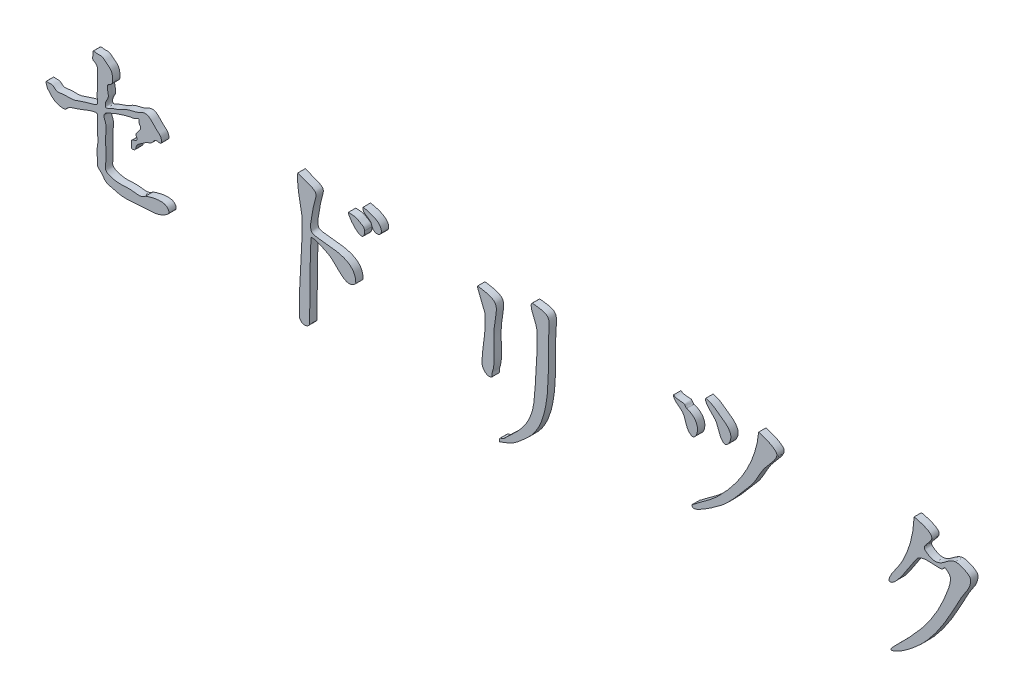
SolidWorks part; units mm, degrees
ref_plane "Plan de face" through (0, 0, 0) normal (0, 0, 1) x (1, 0, 0)
ref_plane "Plan de dessus" through (0, 0, 0) normal (0, 1, 0) x (1, 0, 0)
ref_plane "Plan de droite" through (0, 0, 0) normal (1, 0, 0) x (0, 0, -1)
sketch "Esquisse2" plane through (0, 0, 0) normal (0, 0, 1) x (1, 0, 0)
  line L0 (232.9141, 131.3385) -> (1160.2474, 131.3385) construction
  spline S0 degree 3 poles (432.0808, 148.8385) (430.7718, 149.2574) (428.1607, 149.2105) (428.0808, 147.8385) (426.1031, 113.8895) (427.0708, 79.8306) (426.0808, 45.8385) (425.9892, 42.6952) (421.1449, 40.1314) (418.0808, 40.8385) (415.0863, 41.5295) (412.1299, 44.7657) (412.0808, 47.8385) (411.4511, 87.1894) (416.3283, 126.4834) (416.0808, 165.8385) (416.0785, 166.1982) (407.6157, 203.5133) (410.0808, 215.8385) knots 6 6 6 6 7 7 7 8 8 8 9 9 9 10 10 10 11 11 11 12 12 12 12
  spline S1 degree 3 poles (410.0808, 215.8385) (444.7055, 203.2477) (434.1746, 207.8131) (430.0808, 179.8385) (428.9664, 172.224) (426.3503, 164.337) (428.0808, 156.8385) (430.5024, 146.3446) (489.0808, 160.2947) (489.0808, 124.8385) (489.0808, 124.3671) (488.4141, 124.1718) (488.0808, 123.8385) (475.6539, 111.4116) (464.0342, 132.9607) (453.0808, 139.8385) (446.631, 143.8883) (439.3342, 146.5174) (432.0808, 148.8385) knots 0 0 0 0 1 1 1 2 2 2 3 3 3 4 4 4 5 5 5 6 6 6 6
  spline S2 degree 3 poles (501.0808, 192.8385) (501.0808, 171.0749) (477.8712, 199.0004) (479.0808, 203.8385) knots 2 2 2 2 3 3 3 3
  spline S3 degree 3 poles (479.0808, 203.8385) (487.057, 203.1134) (488.4543, 203.9228) (493.0808, 200.8385) (495.8624, 198.9841) (501.0808, 197.4303) (501.0808, 192.8385) knots 0 0 0 0 1 1 1 2 2 2 2
  spline S4 degree 3 poles (513.0808, 199.8385) (512.205, 200.5391) (510.0802, 206.839) (509.0808, 207.8385) (504.114, 212.8053) (497.4445, 213.2937) (499.0808, 219.8385) knots 2 2 2 2 3 3 3 4 4 4 4
  spline S5 degree 3 poles (499.0808, 219.8385) (504.6438, 219.0438) (513.1693, 216.4461) (517.0808, 213.8385) (530.4477, 204.9272) (521.5423, 193.0693) (513.0808, 199.8385) knots 0 0 0 0 1 1 1 2 2 2 2
  spline S6 degree 3 poles (674.0808, 106.8385) (667.2894, 103.4428) (661.0808, 111.5723) (661.0808, 116.8385) (661.0808, 137.3004) (667.2207, 155.4389) (665.0808, 176.8385) (664.4549, 183.0973) (654.0021, 201.6025) (655.0808, 204.8385) knots 3 3 3 3 4 4 4 5 5 5 6 6 6 6
  spline S7 degree 3 poles (655.0808, 204.8385) (693.7907, 199.9998) (677.0808, 190.2367) (677.0808, 155.8385) (677.0808, 141.4897) (679.6182, 126.451) (675.0808, 112.8385) (674.4396, 110.915) (675.8943, 107.7453) (674.0808, 106.8385) knots 0 0 0 0 1 1 1 2 2 2 3 3 3 3
  spline S8 degree 3 poles (736.0808, 190.8385) (735.8789, 200.2231) (729.0148, 208.4983) (728.0808, 217.8385) (727.9324, 219.3218) (728.5962, 221.9735) (730.0808, 221.8385) (754.1032, 219.6546) (753.4077, 216.0889) (752.0808, 198.8385) (749.2185, 161.6286) (759.794, 94.1709) (724.0808, 60.8385) (704.1065, 42.1958) (701.9448, 42.1625) (685.0808, 35.8385) knots 5 5 5 5 6 6 6 7 7 7 8 8 8 9 9 9 10 10 10 10
  spline S9 degree 3 poles (685.0808, 35.8385) (685.0808, 37.1718) (684.213, 38.8262) (685.0808, 39.8385) (686.536, 41.5362) (689.451, 41.3075) (691.0808, 42.8385) (708.2583, 58.975) (722.0923, 70.4756) (729.0808, 92.8385) (731.6962, 101.208) (732.456, 110.0922) (733.0808, 118.8385) (734.7922, 142.7983) (736.5972, 166.8232) (736.0808, 190.8385) knots 0 0 0 0 1 1 1 2 2 2 3 3 3 4 4 4 5 5 5 5
  spline S10 degree 3 poles (940.0808, 202.8385) (963.1714, 195.1416) (953.7497, 171.1709) (947.0808, 173.8385) (938.4753, 177.2807) (939.3313, 190.0045) (934.0808, 195.8385) (929.9691, 200.4071) (922.0808, 203.6921) (922.0808, 209.8385) knots 3 3 3 3 4 4 4 5 5 5 6 6 6 6
  spline S11 degree 3 poles (922.0808, 209.8385) (923.527, 209.4769) (924.619, 208.1309) (926.0808, 207.8385) (929.3657, 207.1815) (932.7958, 207.4955) (936.0808, 206.8385) (937.9298, 206.4687) (938.2919, 203.4348) (940.0808, 202.8385) knots 0 0 0 0 1 1 1 2 2 2 3 3 3 3
  spline S12 degree 3 poles (992.0808, 186.8385) (984.701, 188.3144) (983.1076, 203.8049) (979.0808, 208.8385) (975.4123, 213.4241) (963.4921, 222.6611) (966.0808, 227.8385) knots 3 3 3 3 4 4 4 5 5 5 5
  spline S13 degree 3 poles (966.0808, 227.8385) (970.8696, 227.0404) (975.5793, 224.4646) (979.0808, 221.8385) (989.3444, 214.1408) (1007.6125, 205.6362) (997.0808, 189.8385) (996.0026, 188.2213) (993.9867, 186.4573) (992.0808, 186.8385) knots 0 0 0 0 1 1 1 2 2 2 3 3 3 3
  spline S14 degree 3 poles (973.0808, 101.8385) (955.3152, 89.9948) (948.0138, 87.1732) (947.0808, 91.8385) (946.8034, 93.2253) (948.9764, 93.955) (950.0808, 94.8385) (960.6506, 103.2943) (972.3486, 110.4307) (982.0808, 119.8385) (1009.9385, 146.7677) (1034.787, 184.3141) (1038.0808, 223.8385) knots 5 5 5 5 6 6 6 7 7 7 8 8 8 9 9 9 9
  spline S15 degree 3 poles (1038.0808, 223.8385) (1045.1995, 221.7029) (1057.4805, 217.9721) (1062.0808, 211.8385) (1066.6736, 205.7148) (1051.0388, 192.4251) (1045.0808, 183.8385) (1038.3328, 174.1135) (1033.929, 162.6994) (1026.0808, 153.8385) (1016.0594, 142.5241) (1006.8695, 130.4237) (996.0808, 119.8385) (989.1315, 113.0204) (981.1811, 107.2387) (973.0808, 101.8385) knots 0 0 0 0 1 1 1 2 2 2 3 3 3 4 4 4 5 5 5 5
  spline S16 degree 3 poles (1224.0808, 64.8385) (1252.2153, 92.2516) (1275.5895, 117.1487) (1291.0808, 153.8385) (1293.5642, 159.7204) (1303.0102, 180.4161) (1298.0808, 185.8385) (1289.2174, 195.5882) (1291.6199, 187.3725) (1287.0808, 186.8385) (1276.4407, 185.5867) (1263.7888, 190.0793) (1255.0808, 183.8385) (1251.0844, 180.9745) (1226.944, 135.7426) (1217.0808, 136.8385) (1214.4098, 137.1353) (1216.85, 142.4495) (1218.0808, 144.8385) (1222.6117, 153.6339) (1229.5921, 161.0214) (1234.0808, 169.8385) (1244.8809, 191.0531) (1248.6675, 207.2262) (1250.0808, 229.8385) knots 8 8 8 8 9 9 9 10 10 10 11 11 11 12 12 12 13 13 13 14 14 14 15 15 15 16 16 16 16
  spline S17 degree 3 poles (1250.0808, 229.8385) (1251.6302, 229.3958) (1274.6718, 224.5227) (1274.0808, 216.8385) (1273.5433, 209.8512) (1259.6339, 202.2479) (1265.0808, 197.8385) (1288.5945, 178.8036) (1294.0532, 211.1568) (1313.0808, 203.8385) (1318.62, 201.708) (1327.2255, 198.7716) (1327.0808, 192.8385) (1326.8081, 181.6615) (1317.1909, 172.7826) (1312.0808, 162.8385) (1297.7982, 135.0455) (1282.3584, 106.7509) (1260.0808, 84.8385) (1257.0039, 81.8121) (1232.7633, 59.3262) (1219.0808, 56.8385) (1215.9868, 56.276) (1221.8285, 62.644) (1224.0808, 64.8385) knots 0 0 0 0 1 1 1 2 2 2 3 3 3 4 4 4 5 5 5 6 6 6 7 7 7 8 8 8 8
  spline S18 degree 3 poles (71.0754, 142.9597) (75.4067, 135.4309) (84.662, 131.0239) (93.2749, 132.3289) knots 0 0 0 0 1 1 1 1
  spline S19 degree 3 poles (93.2749, 132.3289) (97.1532, 137.9943) (107.0232, 139.8388) (120.1737, 145.3167) (127.9688, 148.3887) (138.3028, 150.4256) (136.771, 142.9134) (137.1866, 136.9637) (136.9161, 129.7798) (137.3904, 121.7141) (137.8435, 112.4509) (134.8371, 102.883) (138.1932, 94.7265) (135.799, 86.8932) (143.4968, 82.1954) (146.9939, 74.2276) (157.3244, 71.4208) (169.9252, 67.7133) (185.3121, 68.5902) (201.75, 70.1743) (216.5712, 69.9187) (227.4319, 74.5624) (236.0297, 80.0802) (231.5538, 88.1935) (218.7651, 89.785) (209.2098, 86.8683) (202.3964, 84.4906) knots 0 0 0 0 0.07336 0.118543 0.16439 0.187974 0.211346 0.231206 0.26472 0.294536 0.32805 0.374882 0.408128 0.429266 0.461848 0.498878 0.528382 0.581973 0.65769 0.70748 0.780977 0.826618 0.85646 0.879781 0.914735 1 1 1 1
  spline S20 degree 3 poles (202.3964, 84.4906) (196.734, 79.2036) (186.8378, 82.53) (173.6786, 82.0002) (163.9142, 81.4727) (155.4839, 83.5177) (146.421, 87.3191) (148.9758, 97.4744) (148.0497, 107.1525) (148.5193, 119.0725) (147.7204, 131.0699) (149.9786, 142.4204) (144.3615, 150.6524) (148.1582, 155.8086) (154.5134, 158.5138) (167.0746, 164.1982) (179.314, 167.2655) (187.3883, 168.5985) knots 0 0 0 0 0.117307 0.175749 0.239848 0.290152 0.339314 0.38833 0.451438 0.522183 0.601363 0.669232 0.727309 0.750321 0.773943 0.851674 1 1 1 1
  spline S21 degree 3 poles (187.3883, 168.5985) (196.2298, 174.2771) (191.1457, 167.6523) (199.978, 159.8071) (187.0597, 153.0347) (190.2023, 148.8385) knots 0 0 0 0 0.327364 0.495941 1 1 1 1
  spline S22 degree 3 poles (190.2023, 148.8385) (193.3387, 142.389) (181.2718, 143.9994) (184.4131, 136.4257) (182.1616, 130.9391) (189.6501, 131.1996) (189.0058, 139.1421) (197.0656, 143.265) (203.2616, 149.1195) (212.0301, 151.0312) (215.2835, 159.4468) (225.2575, 154.8041) (224.1233, 165.8054) (217.5191, 170.0218) (212.1757, 176.1595) (206.5673, 181.5877) (199.3617, 182.4369) (192.1214, 177.3901) (182.8145, 176.2414) (173.6317, 172.8451) (165.2368, 167.5216) (157.4161, 166.3092) (146.9187, 159.6995) (147.91, 170.4136) (154.7259, 176.8741) (147.359, 189.9752) (158.2311, 193.3329) (158.051, 202.5342) (155.439, 211.1086) (148.7079, 215.0119) (142.9746, 220.8767) (137.0968, 219.1229) (129.601, 221.5678) (131.4834, 214.9381) (129.2144, 209.7909) (134.5201, 207.8027) (137.26, 204.2058) (136.4939, 198.7873) (136.8659, 191.8017) (136.6572, 183.5805) (136.8882, 174.7733) (136.1795, 167.7582) (138.2608, 159.4742) (130.2322, 157.1068) (122.9766, 155.4859) (112.9262, 151.6753) (102.1458, 148.0622) (90.7294, 149.6403) (81.137, 146.1298) (75.902, 153.2356) (71.4024, 151.8487) (65.8285, 153.5336) (68.4613, 147.0991) (68.5466, 144.4503) (71.0754, 142.9597) knots 0 0 0 0 0.027685 0.040614 0.051927 0.061624 0.079346 0.098807 0.12606 0.146008 0.164292 0.18207 0.200655 0.21952 0.24466 0.263087 0.278525 0.296247 0.328991 0.349703 0.372473 0.402643 0.421299 0.43746 0.45953 0.496806 0.507088 0.536074 0.552579 0.576169 0.594678 0.609223 0.624577 0.634914 0.650421 0.660237 0.672548 0.682885 0.700976 0.727259 0.746653 0.76847 0.784631 0.801981 0.821189 0.845976 0.884233 0.906859 0.935949 0.95173 0.962234 0.972739 0.981931 1 1 1 1
extrude "Boss.-Extru.1" add sketch "Esquisse2" along normal blind 10
